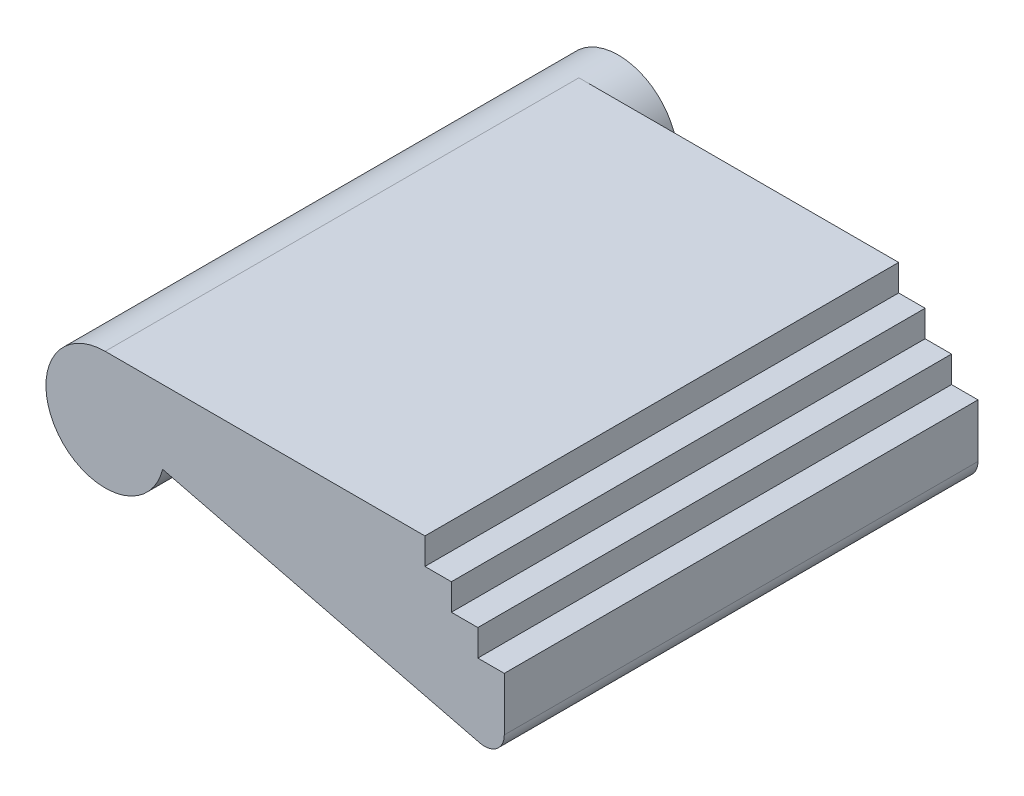
SolidWorks part; units mm, degrees
ref_plane "前视基准面" through (0, 0, 0) normal (0, 0, 1) x (1, 0, 0)
ref_plane "上视基准面" through (0, 0, 0) normal (0, 1, 0) x (1, 0, 0)
ref_plane "右视基准面" through (0, 0, 0) normal (1, 0, 0) x (0, 0, -1)
sketch "草图1" plane through (0, 0, 0) normal (0, 0, 1) x (1, 0, 0)
  circle A0 centre (0, 0) radius 1.5
  dimension "D1" = 3
extrude "凸台-拉伸1" add sketch "草图1" along normal blind 13
sketch "草图2" plane through (0, 0, 13) normal (0, 0, 1) x (1, 0, 0)
  line L0 (0, 1.5) -> (8.1, 1.5)
  line L1 (8.1, 1.5) -> (8.1, 0.83)
  line L2 (8.1, 0.83) -> (8.77, 0.83)
  line L3 (8.77, 0.83) -> (8.77, 0.16)
  line L4 (8.77, 0.16) -> (9.44, 0.16)
  line L5 (9.44, 0.16) -> (9.44, -0.51)
  line L6 (10.11, -2.5) -> (0, 0)
  line L7 (0, 0) -> (0, 1.5)
  line L8 (9.44, -0.51) -> (10.11, -0.51)
  line L9 (10.11, -0.51) -> (10.11, -2.5)
  circle A0 centre (0, 0) radius 1.5 construction
  dimension "D1" = 8.1
  dimension "D2" = 0.67
  dimension "D3" = 0.67
  dimension "D4" = 0.67
  dimension "D5" = 0.67
  dimension "D6" = 0.67
  dimension "D7" = 4
  dimension "D8" = 0.67
extrude "凸台-拉伸2" add sketch "草图2" against normal blind 12
fillet "圆角1" radius 0.5 1 edges at (10.11, -2.5, 7)
